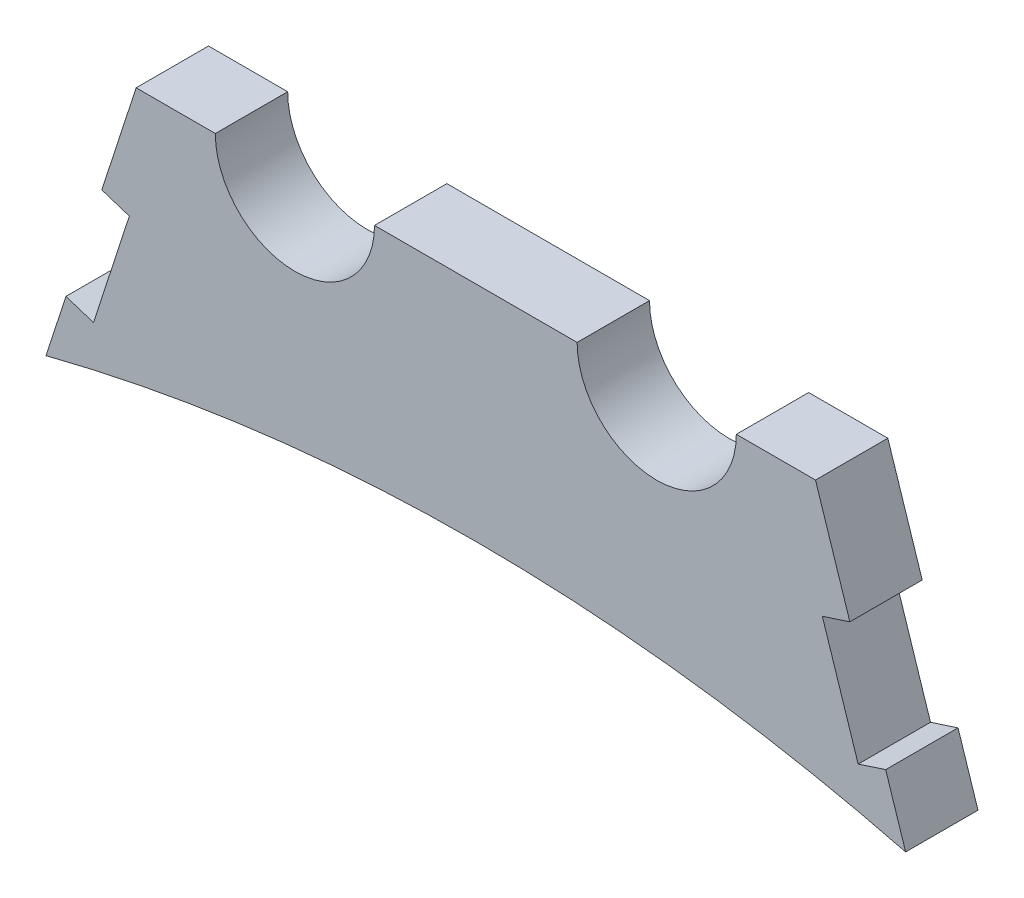
SolidWorks part; units mm, degrees
ref_plane "Front Plane" through (0, 0, 0) normal (0, 0, 1) x (1, 0, 0)
ref_plane "Top Plane" through (0, 0, 0) normal (0, 1, 0) x (1, 0, 0)
ref_plane "Right Plane" through (0, 0, 0) normal (1, 0, 0) x (0, 0, -1)
sketch "Sketch1" plane through (0, 0, 0) normal (0, 0, 1) x (1, 0, 0)
  line L0 (0, 0) -> (0, 324.652) construction
  line L1 (30.7076, 181.3003) -> (24.6961, 151.9943) construction
  line L2 (37.137, 149.4423) -> (40.6988, 166.8059) construction
  line L3 (-37.137, 149.4423) -> (-40.6988, 166.8059) construction
  line L4 (-30.7076, 181.3003) -> (-24.6961, 151.9943) construction
  line L5 (0, 0) -> (-38.8975, 189.6253) construction
  line L6 (27.6276, 178.6698) -> (37.137, 149.4423) construction
  line L7 (0, 0) -> (38.8975, 189.6253) construction
  line L12 (30.2004, 175.8931) -> (45.4337, 129.0731) construction
  line L13 (-27.6276, 178.6698) -> (-37.137, 149.4423) construction
  line L14 (-30.2004, 175.8931) -> (-45.4337, 129.0731) construction
  line L22 (37.7172, 147.659) -> (35.9655, 153.043)
  line L34 (-37.7172, 147.659) -> (-35.9655, 153.043)
  line L39 (-30.4067, 161.9187) -> (-32.822, 162.7045)
  line L40 (-30.4067, 161.9187) -> (-33.5501, 152.2572)
  line L41 (-33.5501, 152.2572) -> (-35.9655, 153.043)
  line L42 (33.5501, 152.2572) -> (35.9655, 153.043)
  line L43 (30.4067, 161.9187) -> (33.5501, 152.2572)
  line L44 (30.4067, 161.9187) -> (32.822, 162.7045)
  line L45 (-32.822, 162.7045) -> (-29.8065, 171.9727)
  line L46 (32.822, 162.7045) -> (29.8065, 171.9727)
  line L47 (-29.8065, 171.9727) -> (-22.86, 171.9727)
  line L48 (29.8065, 171.9727) -> (22.86, 171.9727)
  line L49 (-8.89, 171.9727) -> (8.89, 171.9727)
  circle A0 centre (0, 0) radius 152.4 construction
  circle A1 centre (9.5123, 172.7758) radius 12.7 construction
  circle A2 centre (9.5123, 172.7758) radius 19.05 construction
  circle A3 centre (-15.875, 171.9727) radius 6.35 construction
  circle A4 centre (-15.875, 171.9727) radius 12.7 construction
  circle A5 centre (0, 0) radius 153.9875 construction
  circle A8 centre (0, 149.4423) radius 44.248 construction
  circle A10 centre (0, 149.4423) radius 45.8355 construction
  arc A33 (37.7172, 147.659) -> (-37.7172, 147.659) centre (0, 0) ccw
  circle A38 centre (15.875, 171.9727) radius 12.7 construction
  circle A39 centre (15.875, 171.9727) radius 6.35 construction
  arc A43 (-22.86, 171.9727) -> (-8.89, 171.9727) centre (-15.875, 171.9727) ccw
  arc A44 (22.86, 171.9727) -> (8.89, 171.9727) centre (15.875, 171.9727) cw
  dimension "D1" = 304.8
  dimension "D2" = 25.4
  dimension "D3" = 15.875
  dimension "D4" = 38.1
  dimension "D5" = 12.7
  dimension "D6" = 9.5123
  dimension "D8" = 307.975
  dimension "D7" = 33.5501
  dimension "D11" = 88.496
  dimension "D12" = 91.671
  dimension "D13" = 1.5875
  dimension "D14" = 13.97
  dimension "D9" = 6.35
  dimension "D10" = 6.35
  dimension "D15" = 2.54
  dimension "D16" = 10.16
extrude "Boss-Extrude2" add sketch "Sketch1" along normal blind 6.35
